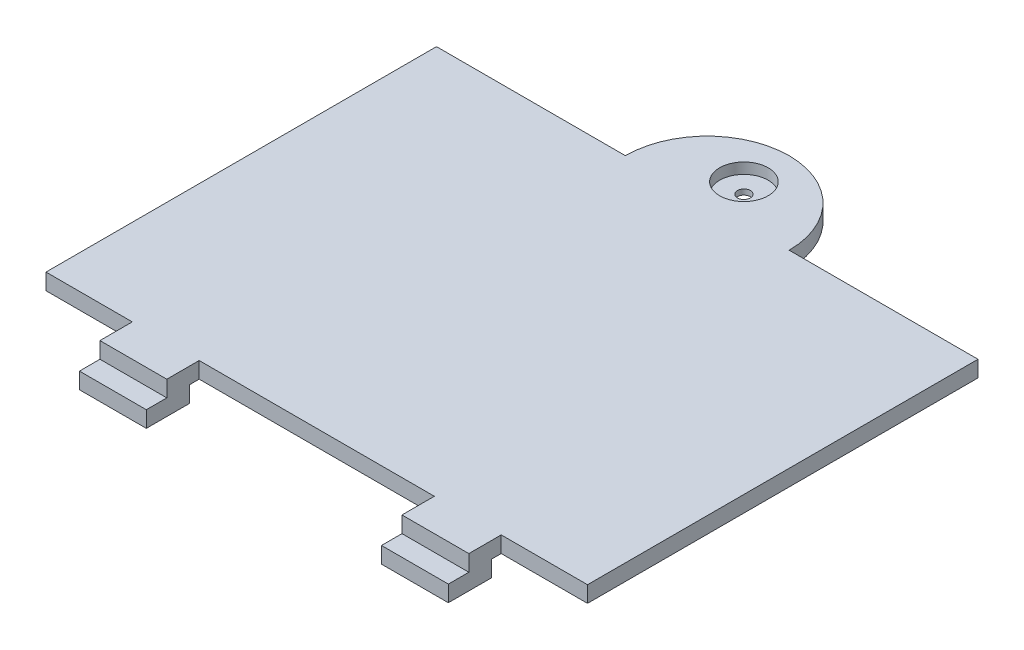
SolidWorks part; units mm, degrees
ref_plane "Front Plane" through (0, 0, 0) normal (0, 0, 1) x (1, 0, 0)
ref_plane "Top Plane" through (0, 0, 0) normal (0, 1, 0) x (1, 0, 0)
ref_plane "Right Plane" through (0, 0, 0) normal (1, 0, 0) x (0, 0, -1)
sketch "Sketch1" plane through (0, 0, 0) normal (0, 1, 0) x (1, 0, 0)
  line L1 (0, 0) -> (-50.2, 0)
  line L2 (0, 0) -> (0, -36.2)
  line L3 (0, -36.2) -> (-50.2, -36.2)
  line L4 (-50.2, 0) -> (-50.2, -36.2)
  dimension "D1" = 36.2
  dimension "D2" = 50.2
extrude "Boss-Extrude1" add sketch "Sketch1" along normal blind 1.5
sketch "Sketch2" plane through (0, 0, 36.2) normal (0, 0, 1) x (1, 0, 0)
  line L0 (-50.2, 0) -> (0, 0) construction
  line L1 (-42.2, 0) -> (-36, 0)
  line L2 (-42.2, 0) -> (-42.2, 1.5)
  line L3 (-42.2, 1.5) -> (-36, 1.5)
  line L4 (-36, 0) -> (-36, 1.5)
  line L5 (-50.2, 1.5) -> (-50.2, 0) construction
  line L6 (-14.2, 0) -> (-8, 0)
  line L7 (-14.2, 0) -> (-14.2, 1.5)
  line L8 (-14.2, 1.5) -> (-8, 1.5)
  line L9 (-8, 0) -> (-8, 1.5)
  line L10 (0, 1.5) -> (0, 0) construction
  point P14 (-8, 0.75)
  dimension "D1" = 8
  dimension "D2" = 8
  dimension "D3" = 6.2
  dimension "D4" = 1.5
  dimension "D5" = 6.2
  dimension "D6" = 6.2
  dimension "D7" = 1.5
extrude "Boss-Extrude2" add sketch "Sketch2" along normal blind 3
sketch "Sketch4" plane through (0, 1.5, 0) normal (0, 1, 0) x (1, 0, 0)
  line L0 (0, 0) -> (-50.2, 0) construction
  line L1 (0, 0) -> (-17.51, 0)
  line L2 (-17.51, 0) -> (-32.69, 0)
  line L5 (0, -36.2) -> (0, 0)
  line L6 (0, 0) -> (-50.2, 0)
  line L7 (-50.2, 0) -> (-50.2, -36.2)
  line L8 (-50.2, -36.2) -> (-42.2, -36.2)
  line L9 (0, -36.2) -> (0, 0)
  line L10 (-32.69, 0) -> (-50.2, 0)
  line L11 (-50.2, 0) -> (-50.2, -36.2)
  line L12 (-50.2, -36.2) -> (-42.2, -36.2)
  line L23 (-42.2, -36.2) -> (-42.2, -39.2)
  line L24 (-42.2, -36.2) -> (-42.2, -39.2)
  line L25 (-42.2, -39.2) -> (-36, -39.2)
  line L26 (-42.2, -39.2) -> (-36, -39.2)
  line L27 (-36, -39.2) -> (-36, -36.2)
  line L28 (-36, -39.2) -> (-36, -36.2)
  line L29 (-36, -36.2) -> (-14.2, -36.2)
  line L30 (-36, -36.2) -> (-14.2, -36.2)
  line L31 (-14.2, -36.2) -> (-14.2, -39.2)
  line L32 (-14.2, -36.2) -> (-14.2, -39.2)
  line L33 (-14.2, -39.2) -> (-8, -39.2)
  line L34 (-14.2, -39.2) -> (-8, -39.2)
  line L35 (-8, -39.2) -> (-8, -36.2)
  line L36 (-8, -39.2) -> (-8, -36.2)
  line L37 (-8, -36.2) -> (0, -36.2)
  line L38 (-8, -36.2) -> (0, -36.2)
  arc A0 (-32.69, 0) -> (-17.51, 0) centre (-25.1, 0) cw
  line M2 (0, 0) -> (-50.2, 0)
  dimension "D1" = 7.59
  dimension "D2" = 0
extrude "Boss-Extrude3" add sketch "Sketch4" against normal blind 1.5 contours A0 M2
sketch "Sketch5" plane through (0, 1.5, 0) normal (0, 1, 0) x (1, 0, 0)
  circle A0 centre (-25.1, 3.4) radius 2.25
  arc A2 (-17.51, 0) -> (-32.69, 0) centre (-25.1, 0) ccw construction
  point P5 (-25.1, 7.59)
  dimension "D1" = 4.5
  dimension "D2" = 3.4
extrude "Cut-Extrude1" cut sketch "Sketch5" against normal blind 1
sketch "Sketch6" plane through (0, 0.5, 0) normal (0, 1, 0) x (1, 0, 0)
  circle A0 centre (-25.1, 3.4) radius 0.6
  dimension "D1" = 1.2
extrude "Cut-Extrude2" cut sketch "Sketch6" against normal blind 1
sketch "Sketch8" plane through (0, 1.5, 0) normal (0, 1, 0) x (1, 0, 0)
  line L0 (-28.2268, -7) -> (-21.9732, -7)
  line L1 (-21.9232, -7.1866) -> (-25.05, -8.9919)
  line L2 (-25.15, -8.9919) -> (-28.2768, -7.1866)
  line L3 (-32.69, 0) -> (-50.2, 0) construction
  line L4 (-28.5268, -4) -> (-21.6732, -4)
  line L5 (-28.2268, -6) -> (-21.9732, -6)
  line L6 (-28.5268, -5.7) -> (-28.5268, -5)
  line L7 (-28.5268, -5) -> (-21.6732, -5)
  line L8 (-21.6732, -5.7) -> (-21.6732, -5)
  line L9 (-28.8268, -3.7) -> (-28.8268, -3)
  line L10 (-28.8268, -3) -> (-21.3732, -3)
  line L11 (-21.3732, -3.7) -> (-21.3732, -3)
  circle A0 centre (-25.1, 3.4) radius 2.25 construction
  circle A1 centre (-25.1, 3.4) radius 2.25
  arc A2 (-21.9732, -6) -> (-21.6732, -5.7) centre (-21.9732, -5.7) ccw
  arc A3 (-28.5268, -5.7) -> (-28.2268, -6) centre (-28.2268, -5.7) ccw
  arc A4 (-21.6732, -4) -> (-21.3732, -3.7) centre (-21.6732, -3.7) ccw
  arc A5 (-28.8268, -3.7) -> (-28.5268, -4) centre (-28.5268, -3.7) ccw
  arc A6 (-28.2268, -7) -> (-28.2768, -7.1866) centre (-28.2268, -7.1) ccw
  arc A7 (-25.05, -8.9919) -> (-25.15, -8.9919) centre (-25.1, -8.9053) cw
  arc A8 (-21.9732, -7) -> (-21.9232, -7.1866) centre (-21.9732, -7.1) cw
  point P7 (-25.1, -7)
  point P13 (-25.1, -5)
  point P19 (-25.1, -4)
  point P29 (-28.6, -7)
  point P34 (-21.6, -7)
  dimension "D8" = 0.3
  dimension "D9" = 0.1
  dimension "D10" = 0.1
  dimension "D1" = 120
  dimension "D2" = 7
  dimension "D3" = 7
  dimension "D4" = 1
  dimension "D5" = 1
  dimension "D6" = 1
  dimension "D7" = 1
extrude "Cut-Extrude3" [suppressed] cut sketch "Sketch8" against normal blind 0.5 contours L5 L8 L7 L6 | L2 L1 L0 | L10 L11 A4 L4 A5 L9
fillet "Fillet1" [suppressed] radius 0.2
sketch "Sketch9" plane through (0, 0, 0) normal (0, -1, 0) x (1, 0, 0)
  line L0 (-36, 39.2) -> (-36, 36.2) construction
  line L1 (-36, 37.1) -> (-42.2, 37.1)
  line L2 (-36, 37.1) -> (-36, 41.1)
  line L3 (-36, 41.1) -> (-42.2, 41.1)
  line L4 (-42.2, 37.1) -> (-42.2, 41.1)
  line L5 (-8, 39.2) -> (-8, 36.2) construction
  line L6 (-8, 37.1) -> (-14.2, 37.1)
  line L7 (-8, 37.1) -> (-8, 41.1)
  line L8 (-8, 41.1) -> (-14.2, 41.1)
  line L9 (-14.2, 37.1) -> (-14.2, 41.1)
  line L10 (-14.2, 39.2) -> (-14.2, 36.2) construction
  line L11 (-42.2, 39.2) -> (-42.2, 36.2) construction
  line L13 (-50.2, 36.2) -> (-42.2, 36.2) construction
  dimension "D1" = 0.9
  dimension "D2" = 4
extrude "Boss-Extrude4" add sketch "Sketch9" along normal blind 1.5
